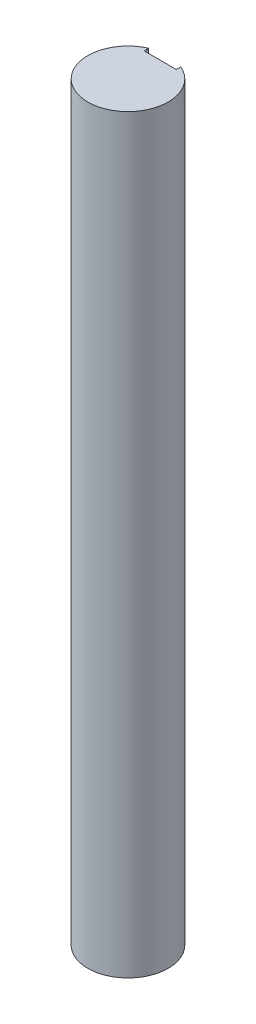
SolidWorks part; units mm, degrees
ref_plane "Front Plane" through (0, 0, 0) normal (0, 0, 1) x (1, 0, 0)
ref_plane "Top Plane" through (0, 0, 0) normal (0, 1, 0) x (1, 0, 0)
ref_plane "Right Plane" through (0, 0, 0) normal (1, 0, 0) x (0, 0, -1)
sketch "Sketch1" plane through (0, 0, 0) normal (0, 1, 0) x (1, 0, 0)
  circle A0 centre (0, 0) radius 3.75
  dimension "D1" = 7.5
extrude "Boss-Extrude1" add sketch "Sketch1" along normal blind 70
sketch "Sketch2" plane through (0, 70, 0) normal (0, 1, 0) x (1, 0, 0)
  line L0 (0, 0) -> (0, 3.75) construction
  line L1 (0, 3.0105) -> (-1.5, 3.0105)
  line L2 (-1.5, 3.0105) -> (-1.5, 3.75)
  line L3 (0, 3.0105) -> (1.5, 3.0105)
  line L4 (1.5, 3.0105) -> (1.5, 3.75)
  line L5 (-1.5, 3.75) -> (1.5, 3.75)
  circle A0 centre (0, 0) radius 3.75 construction
  circle A1 centre (0, 0) radius 3 construction
  point P10 (0, 3.2395)
  point P11 (0, 3.0105)
  dimension "D4" = 6
  dimension "D1" = 3
  dimension "D2" = 1.5
  dimension "D3" = 0
extrude "Cut-Extrude1" cut sketch "Sketch2" against normal through all
